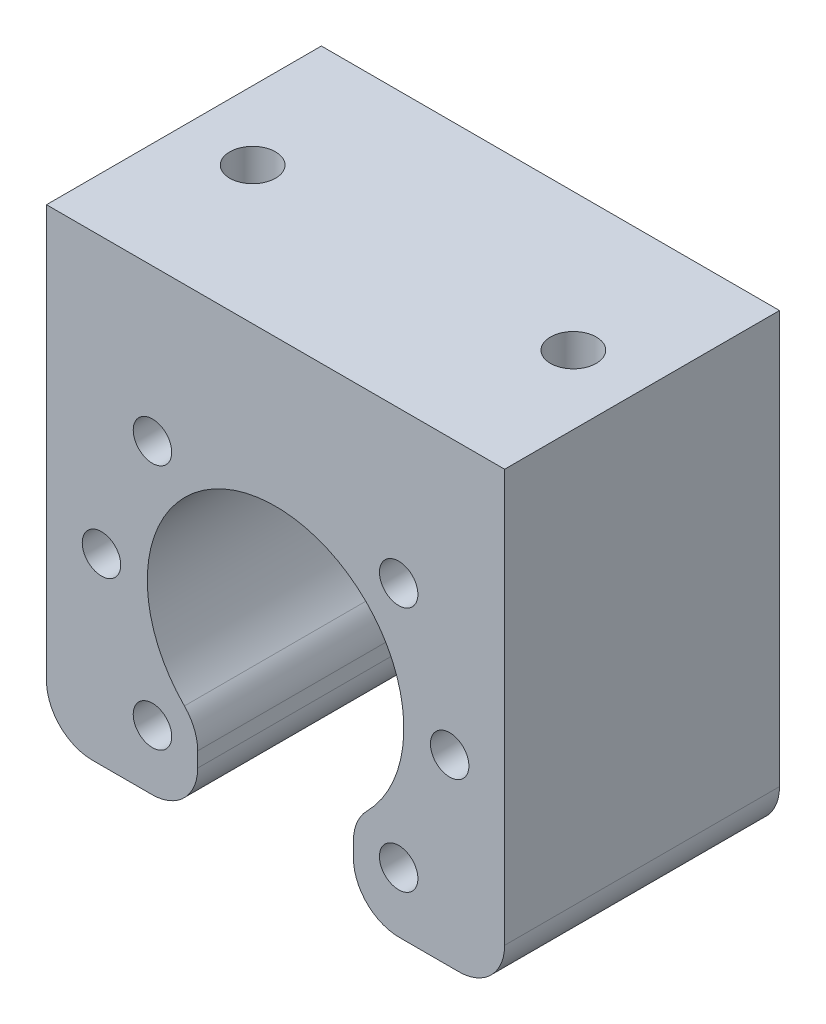
SolidWorks part; units mm, degrees
material "1023 Листовая углеродистая сталь (SS)"
ref_plane "Front" through (0, 0, 0) normal (0, 0, 1) x (1, 0, 0)
ref_plane "Top" through (0, 0, 0) normal (0, 1, 0) x (1, 0, 0)
ref_plane "Right" through (0, 0, 0) normal (1, 0, 0) x (0, 0, -1)
sketch "Sketch1" plane through (0, 0, 0) normal (0, 0, 1) x (1, 0, 0)
  line L0 (0, 0) -> (0, 30) construction
  line L1 (-25, 30) -> (25, 30)
  line L2 (-25, 30) -> (-25, -20)
  line L3 (-25, -20) -> (-8.5, -20)
  line L4 (25, 30) -> (25, -20)
  line L5 (8.5, -20) -> (25, -20)
  line L7 (-8.5, -11.1243) -> (-8.5, -20)
  line L9 (8.5, -11.1243) -> (8.5, -20)
  arc A0 (8.5, -11.1243) -> (-8.5, -11.1243) centre (0, 0) ccw
  dimension "D1" = 28
  dimension "D4" = 6
  dimension "D2" = 50
  dimension "D3" = 30
  dimension "D7" = 8.5
extrude "Extrude1" add sketch "Sketch1" along normal blind 30
fillet "Fillet1" radius 5 6 edges at (-8.5, -20, 15) (8.5, -20, 15) (8.5, -11.1243, 15) (-8.5, -11.1243, 15) (-25, -20, 15) (25, -20, 15)
hole_wizard "M5 Tapped Hole1" positions "Sketch2" profile "Sketch3" tap size "M5" standard "DIN" end condition through all
sketch "Sketch2" plane through (0, 0, 0) normal (0, 0, -1) x (-1, 0, 0)
  point P0 (-13.435, 13.435)
  point P3 (13.435, 13.435)
  point P6 (19, 0)
  point P9 (13.435, -13.435)
  point P12 (-13.435, -13.435)
  point P15 (-19, 0)
sketch "Sketch3" plane through (13.435, 13.435, 0) normal (1, 0, 0) x (0, 1, 0)
  line L0 (0, 0) -> (0, 30)
  line L1 (0, 30) -> (2.1, 30)
  line L2 (2.1, 30) -> (2.1, 0)
  line L5 (2.1, 0) -> (0, 0)
  line L11 (0, -6.35) -> (0, 107.95) construction
  dimension "Диаметр проходного сверла" = 4.2
  dimension "Глубина проходного сверла" = 30
cosmetic thread "Cosmetic Thread1" parameters "D2"=5
cosmetic thread "Cosmetic Thread2" parameters "D2"=5
cosmetic thread "Cosmetic Thread3" parameters "D2"=5
cosmetic thread "Cosmetic Thread4" parameters "D2"=5
cosmetic thread "Cosmetic Thread5" parameters "D2"=5
cosmetic thread "Cosmetic Thread6" parameters "D2"=5
hole_wizard "M6 Tapped Hole1" positions "Sketch4" profile "Sketch6" tap size "M6" standard "DIN"
sketch "Sketch4" plane through (0, 30, 0) normal (0, 1, 0) x (1, 0, 0)
  point P0 (-17.5, -15)
  point P3 (17.5, -15)
sketch "Sketch6" plane through (-17.5, 30, 15) normal (1, 0, 0) x (0, 0, 1)
  line L0 (0, 0) -> (0, 21.5022)
  line L1 (0, 21.5022) -> (2.5, 20)
  line L2 (2.5, 20) -> (2.5, 0)
  line L5 (2.5, 0) -> (0, 0)
  line L10 (0, 21.5022) -> (-2.5, 20) construction
  line L11 (0, -6.35) -> (0, 107.95) construction
  dimension "Диаметр сверла" = 5
  dimension "Глубина сверла" = 20
  dimension "Угол заточки сверла" = 118
cosmetic thread "Cosmetic Thread7" parameters "D1"=12, "D2"=6
cosmetic thread "Cosmetic Thread8" parameters "D1"=12, "D2"=6
